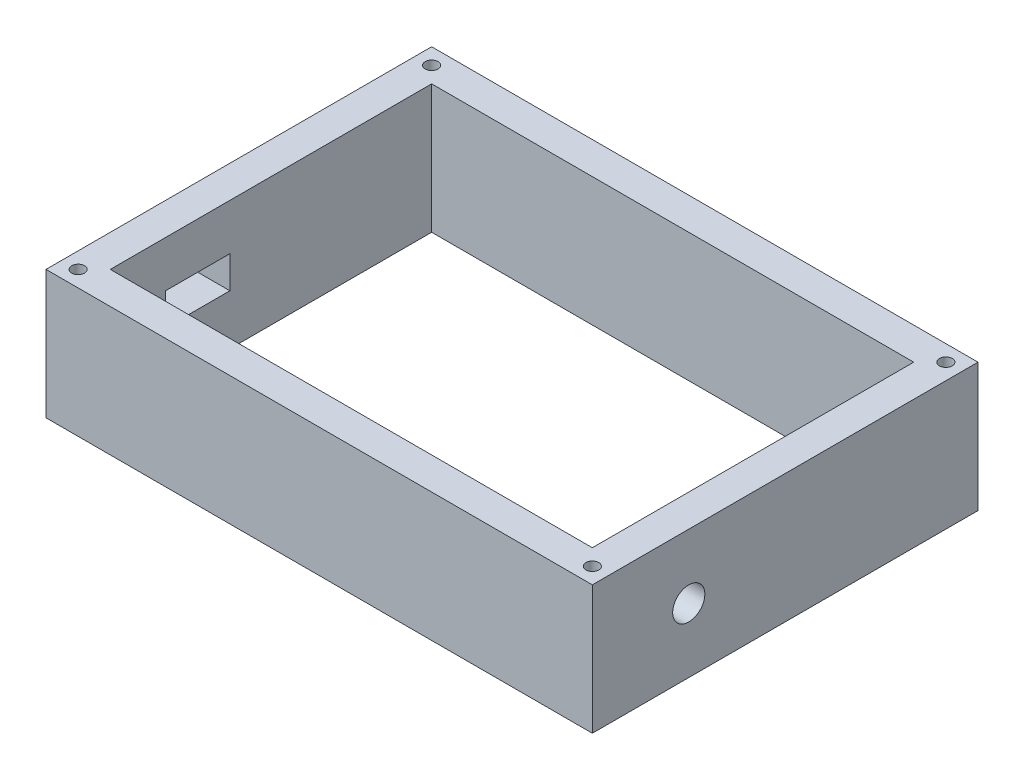
SolidWorks part; units mm, degrees
ref_plane "Front Plane" through (0, 0, 0) normal (0, 0, 1) x (1, 0, 0)
ref_plane "Top Plane" through (0, 0, 0) normal (0, 1, 0) x (1, 0, 0)
ref_plane "Right Plane" through (0, 0, 0) normal (1, 0, 0) x (0, 0, -1)
sketch "Sketch1" plane through (0, 0, 0) normal (0, 1, 0) x (1, 0, 0)
  line L1 (75, -50) -> (-75, -50)
  line L2 (75, -50) -> (75, 50)
  line L3 (75, 50) -> (-75, 50)
  line L4 (-75, -50) -> (-75, 50)
  line L5 (75, -50) -> (-75, 50) construction
  line L6 (75, 50) -> (-75, -50) construction
  point P0 (0, 0)
  dimension "D1" = 150
  dimension "D2" = 100
extrude "Extrude-Thin1" add sketch "Sketch1" along normal blind 40 thin contours L3 L4 L1 L2 thin type one direction wall 10
sketch "Sketch2" plane through (85, 0, 0) normal (1, 0, 0) x (0, 0, -1)
  line L2 (-60, 40) -> (-60, 0) construction
  line L3 (-60, 0) -> (60, 0) construction
  circle A0 centre (-30, 20) radius 5
  point P2 (0, 0)
  point P3 (-26.2002, 20.5166)
  point P4 (0, 0)
  point P6 (0, 0)
  point P7 (0, 0)
  dimension "D1" = 30
  dimension "D2" = 20
extrude "Cut-Extrude1" cut sketch "Sketch2" against normal blind 10 contours A0
sketch "Sketch3" plane through (0, 40, 0) normal (0, 1, 0) x (1, 0, 0)
  line L0 (-85, -60) -> (-85, 60) construction
  line L1 (85, 60) -> (-85, 60) construction
  line L2 (85, -60) -> (-85, -60) construction
  line L3 (85, -60) -> (85, 60) construction
  circle A0 centre (-80, 55) radius 2
  circle A1 centre (-80, -55) radius 2
  circle A2 centre (80, -55) radius 2
  circle A3 centre (80, 55) radius 2
  point P16 (0, 0)
  point P17 (0, 0)
  point P18 (0, 0)
  point P19 (0, 0)
  point P20 (0, 0)
  dimension "D1" = 5
  dimension "D5" = 5
  dimension "D6" = 5
  dimension "D2" = 170
  dimension "D3" = 170
  dimension "D4" = 5
hole_wizard "Ø4.0mm Dowel Hole1" positions "Sketch7" profile "Sketch8" hole size "Ø4.0" standard "ANSI Metric"
sketch "Sketch7" plane through (0, 40, 0) normal (0, 1, 0) x (1, 0, 0)
  point P0 (-80, 55)
sketch "Sketch8" plane through (-80, 40, -55) normal (1, 0, 0) x (0, 0, 1)
  line L0 (0, 0) -> (0, 6.2017)
  line L1 (0, 6.2017) -> (2, 5)
  line L2 (2, 5) -> (2, 0)
  line L5 (2, 0) -> (0, 0)
  line L10 (0, 6.2017) -> (-2, 5) construction
  line L11 (0, -6.35) -> (0, 107.95) construction
  dimension "Hole Dia." = 4
  dimension "Hole Depth" = 5
  dimension "Drill Angle" = 118
hole_wizard "Ø4.0mm Dowel Hole2" positions "Sketch9" profile "Sketch10" hole size "Ø4.0" standard "ANSI Metric"
sketch "Sketch9" plane through (0, 40, 0) normal (0, 1, 0) x (1, 0, 0)
  point P0 (-80, -55)
sketch "Sketch10" plane through (-80, 40, 55) normal (1, 0, 0) x (0, 0, 1)
  line L0 (0, 0) -> (0, 6.2017)
  line L1 (0, 6.2017) -> (2, 5)
  line L2 (2, 5) -> (2, 0)
  line L5 (2, 0) -> (0, 0)
  line L10 (0, 6.2017) -> (-2, 5) construction
  line L11 (0, -6.35) -> (0, 107.95) construction
  dimension "Hole Dia." = 4
  dimension "Hole Depth" = 5
  dimension "Drill Angle" = 118
hole_wizard "Ø4.0mm Dowel Hole3" positions "Sketch11" profile "Sketch12" hole size "Ø4.0" standard "ANSI Metric"
sketch "Sketch11" plane through (0, 40, 0) normal (0, 1, 0) x (1, 0, 0)
  point P0 (80, -55)
sketch "Sketch12" plane through (80, 40, 55) normal (1, 0, 0) x (0, 0, 1)
  line L0 (0, 0) -> (0, 6.2017)
  line L1 (0, 6.2017) -> (2, 5)
  line L2 (2, 5) -> (2, 0)
  line L5 (2, 0) -> (0, 0)
  line L10 (0, 6.2017) -> (-2, 5) construction
  line L11 (0, -6.35) -> (0, 107.95) construction
  dimension "Hole Dia." = 4
  dimension "Hole Depth" = 5
  dimension "Drill Angle" = 118
hole_wizard "Ø4.0mm Dowel Hole4" positions "Sketch13" profile "Sketch14" hole size "Ø4.0" standard "ANSI Metric"
sketch "Sketch13" plane through (0, 40, 0) normal (0, 1, 0) x (1, 0, 0)
  point P0 (80, 55)
sketch "Sketch14" plane through (80, 40, -55) normal (1, 0, 0) x (0, 0, 1)
  line L0 (0, 0) -> (0, 6.2017)
  line L1 (0, 6.2017) -> (2, 5)
  line L2 (2, 5) -> (2, 0)
  line L5 (2, 0) -> (0, 0)
  line L10 (0, 6.2017) -> (-2, 5) construction
  line L11 (0, -6.35) -> (0, 107.95) construction
  dimension "Hole Dia." = 4
  dimension "Hole Depth" = 5
  dimension "Drill Angle" = 118
sketch "Sketch15" plane through (-85, 0, 0) normal (-1, 0, 0) x (0, 0, 1)
  line L1 (12.7853, 25.6312) -> (32.7853, 25.6312)
  line L2 (12.7853, 25.6312) -> (12.7853, 15.6312)
  line L3 (12.7853, 15.6312) -> (32.7853, 15.6312)
  line L4 (32.7853, 25.6312) -> (32.7853, 15.6312)
  line L5 (12.7853, 25.6312) -> (32.7853, 15.6312) construction
  line L6 (12.7853, 15.6312) -> (32.7853, 25.6312) construction
  point P0 (22.7853, 20.6312)
  dimension "D1" = 20
  dimension "D2" = 10
extrude "Cut-Extrude7" cut sketch "Sketch15" against normal blind 10
